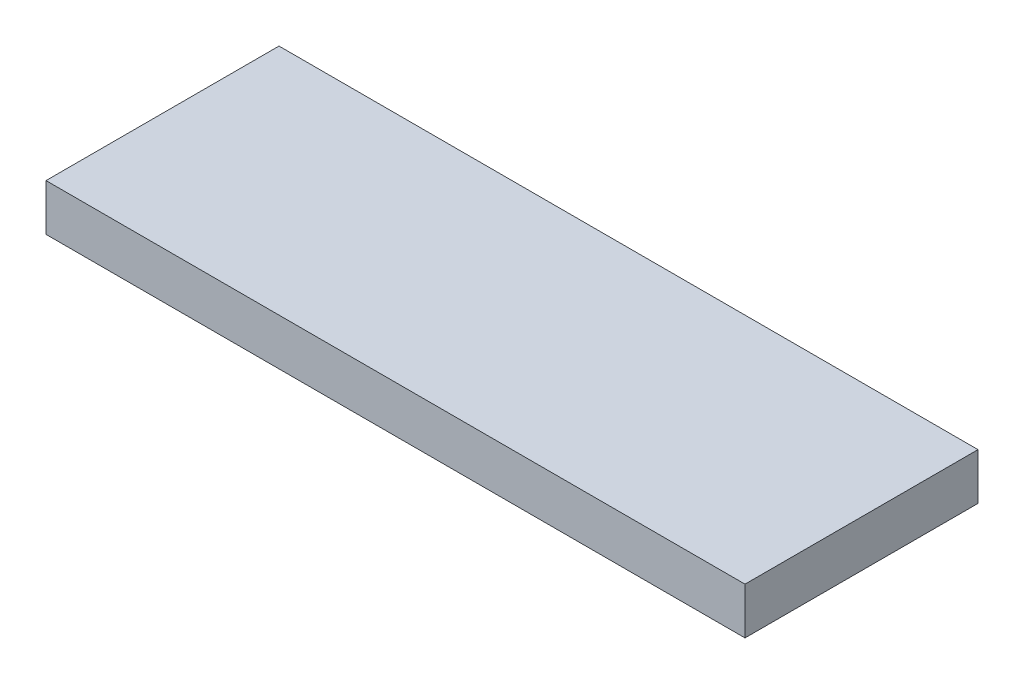
SolidWorks part; units mm, degrees
ref_plane "Спереди" through (0, 0, 0) normal (0, 0, 1) x (1, 0, 0)
ref_plane "Сверху" through (0, 0, 0) normal (0, 1, 0) x (1, 0, 0)
ref_plane "Справа" through (0, 0, 0) normal (1, 0, 0) x (0, 0, -1)
sketch "Эскиз1" plane through (0, 0, 0) normal (0, 1, 0) x (1, 0, 0)
  line L1 (15, -5) -> (-15, -5)
  line L2 (15, -5) -> (15, 5)
  line L3 (15, 5) -> (-15, 5)
  line L4 (-15, -5) -> (-15, 5)
  line L5 (15, -5) -> (-15, 5) construction
  line L6 (15, 5) -> (-15, -5) construction
  point P0 (0, 0)
  dimension "D1" = 10
  dimension "D2" = 30
extrude "Бобышка-Вытянуть1" add sketch "Эскиз1" along normal blind 2
